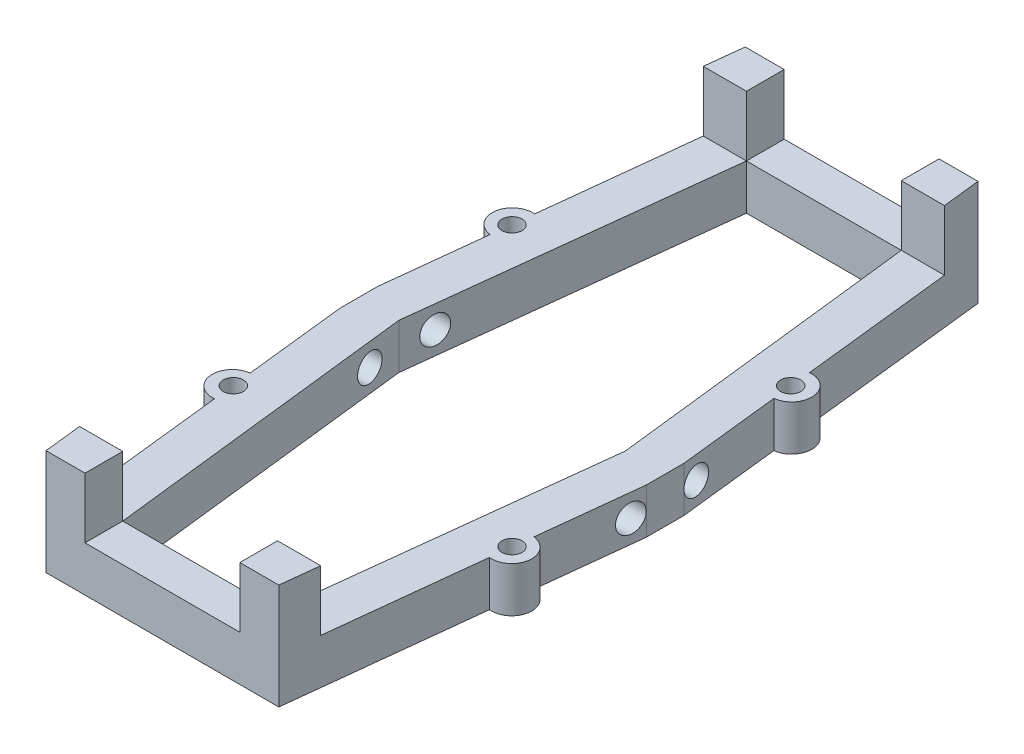
SolidWorks part; units mm, degrees
material "CARBON FIBER TEST"
ref_plane "Front Plane" through (0, 0, 0) normal (0, 0, 1) x (1, 0, 0)
ref_plane "Top Plane" through (0, 0, 0) normal (0, 1, 0) x (1, 0, 0)
ref_plane "Right Plane" through (0, 0, 0) normal (1, 0, 0) x (0, 0, -1)
sketch "Sketch1" plane through (0, 0, 0) normal (0, 1, 0) x (1, 0, 0)
  line L0 (0, 0) -> (0, -34.75) construction
  line L1 (0, -34.75) -> (5.65, 0) construction
  line L2 (5.65, 0) -> (0, 0) construction
  line L3 (5.65, -1.875) -> (5.65, 1.875)
  line L6 (5.65, 1.875) -> (1.9, 1.875)
  line L7 (1.9, 1.875) -> (-1.875, -31)
  line L9 (-1.875, -31) -> (-17.265, -31)
  line L12 (-9.57, 6.0461) -> (-9.57, -44.986) construction
  line L21 (0, -34.75) -> (2, -34.75)
  line L22 (-19.14, -34.75) -> (0, -34.75)
  line L23 (2, -34.75) -> (4.0923, -15.9051)
  line L26 (-24.79, 0) -> (-19.14, 0) construction
  line L27 (-19.14, -34.75) -> (-24.79, 0) construction
  line L28 (-19.14, 0) -> (-19.14, -34.75) construction
  line L30 (-19.14, -34.75) -> (-21.14, -34.75)
  line L31 (-21.04, 1.875) -> (-17.265, -31)
  line L32 (-24.79, 1.875) -> (-21.04, 1.875)
  line L33 (-24.79, -1.875) -> (-24.79, 1.875)
  line L34 (4.5337, -11.9296) -> (5.65, -1.875)
  line L35 (-21.14, -34.75) -> (-23.2323, -15.9051)
  line L36 (-23.6737, -11.9296) -> (-24.79, -1.875)
  arc A0 (4.0923, -15.9051) -> (4.5337, -11.9296) centre (4.313, -13.9174) ccw
  arc A1 (-23.2323, -15.9051) -> (-23.6737, -11.9296) centre (-23.453, -13.9174) cw
  point P7 (5.65, 0)
  point P10 (0, -34.75)
  point P19 (-9.57, -34.75)
  point P20 (-9.57, -34.75)
  point P21 (-9.57, -31)
  point P22 (-9.57, -31)
  point P24 (-19.14, -34.75)
  point P25 (-24.79, 0)
  point P26 (7.9481, -13.85)
  dimension "D11" = 2
  dimension "D1" = 2
  dimension "D2" = 5.65
  dimension "D3" = 3.75
  dimension "D4" = 9.57
  dimension "D5" = 3.75
  dimension "D6" = 7.695
  dimension "D7" = 32.875
  dimension "D8" = 3.75
  dimension "D9" = 33.091
  dimension "D10" = 13.85
  dimension "D12" = 13.9174
extrude "Boss-Extrude1" add sketch "Sketch1" along normal blind 4.5
sketch "Sketch7" plane through (0, 4.5, 0) normal (0, 1, 0) x (1, 0, 0)
  line L8 (-9.57, -20.6242) -> (-9.57, -37.1202) construction
  line L21 (-1.875, -31) -> (-17.265, -31) construction
  line L26 (-1.875, -31) -> (-1.875, -34.75)
  line L27 (-21.14, -34.75) -> (2, -34.75) construction
  line L28 (-1.875, -34.75) -> (2, -34.75)
  line L29 (2, -34.75) -> (2.4163, -31)
  line L30 (2, -34.75) -> (4.0923, -15.9051) construction
  line L31 (2.4163, -31) -> (-1.875, -31)
  line L32 (-21.5563, -31) -> (-17.265, -31)
  line L33 (-21.14, -34.75) -> (-21.5563, -31)
  line L34 (-17.265, -34.75) -> (-21.14, -34.75)
  line L35 (-17.265, -31) -> (-17.265, -34.75)
  point P14 (-9.57, -31)
extrude "Boss-Extrude5" add sketch "Sketch7" along normal blind 6
sketch "Sketch8" plane through (0, 0, 0) normal (0, 1, 0) x (1, 0, 0)
  line L0 (5.65, -1.875) -> (5.65, 1.875) construction
  line L3 (-24.79, 1.875) -> (-24.79, -1.875) construction
  line L5 (-23.42, -13.85) -> (4.28, -13.85) construction
  line L6 (-23.42, -13.85) -> (-23.42, 13.85) construction
  line L7 (-23.42, 13.85) -> (4.28, 13.85) construction
  line L8 (4.28, -13.85) -> (4.28, 13.85) construction
  line L9 (-23.42, -13.85) -> (4.28, 13.85) construction
  line L10 (-23.42, 13.85) -> (4.28, -13.85) construction
  point P4 (5.65, 0)
  point P9 (-9.57, 0)
  dimension "D1" = 27.7
  dimension "D2" = 15.22
  dimension "D3" = 15.22
  dimension "D4" = 13.85
sketch "Sketch9" plane through (0, 4.5, 0) normal (0, 1, 0) x (1, 0, 0)
  circle A0 centre (4.28, 13.85) radius 1
  circle A1 centre (-23.42, 13.85) radius 1
  circle A2 centre (-23.42, -13.85) radius 1
  circle A3 centre (4.28, -13.85) radius 1
  dimension "D1" = 2
extrude "Cut-Extrude2" cut sketch "Sketch9" against normal blind 10
mirror "Mirror1" about plane through (0, 0, 0) normal (0, 0, 1) of "Boss-Extrude1", "Boss-Extrude5", "Cut-Extrude2"
sketch "Sketch11" plane through (5.65, 0, 0) normal (1, 0, 0) x (0, 0, -1)
  line L0 (0, 4.5) -> (0, 0) construction
  line L1 (13.85, 0) -> (-13.85, 0) construction
  line L2 (-1.875, 4.5) -> (1.875, 4.5) construction
  circle A0 centre (-3.25, 2.25) radius 1.375
  circle A1 centre (3.25, 2.25) radius 1.375
  point P6 (0, 2.25)
  dimension "D2" = 2.75
  dimension "D1" = 3.25
  dimension "D3" = 3.25
extrude "Cut-Extrude3" cut sketch "Sketch11" against normal through all both and the other way through all
